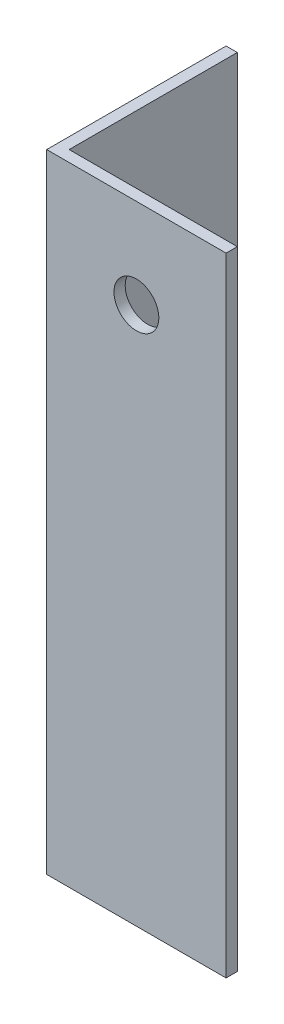
SolidWorks part; units mm, degrees
ref_plane "Front Plane" through (0, 0, 0) normal (0, 0, 1) x (1, 0, 0)
ref_plane "Top Plane" through (0, 0, 0) normal (0, 1, 0) x (1, 0, 0)
ref_plane "Right Plane" through (0, 0, 0) normal (1, 0, 0) x (0, 0, -1)
sketch "Sketch1" plane through (0, 0, 0) normal (0, 1, 0) x (1, 0, 0)
  line L0 (0, 0) -> (0, 25.4)
  line L1 (0, 25.4) -> (1.5875, 25.4)
  line L2 (1.5875, 25.4) -> (1.5875, 1.5875)
  line L3 (1.5875, 1.5875) -> (25.4, 1.5875)
  line L4 (25.4, 1.5875) -> (25.4, 0)
  line L5 (25.4, 0) -> (0, 0)
  dimension "D1" = 1.5875
  dimension "D2" = 25.4
extrude "Boss-Extrude1" add sketch "Sketch1" along normal blind 88.9
sketch "Sketch2" plane through (0, 0, 0) normal (-1, 0, 0) x (0, 0, 1)
  line L0 (-25.4, 0) -> (0, 0) construction
  line L1 (-25.4, 88.9) -> (-25.4, 0) construction
  circle A0 centre (-12.7, 38.1) radius 2.54
  circle A1 centre (-12.7, 12.7) radius 2.54
  dimension "D1" = 12.7
  dimension "D4" = 5.08
  dimension "D2" = 25.4
  dimension "D3" = 12.7
extrude "Cut-Extrude1" cut sketch "Sketch2" against normal blind 88.9
sketch "Sketch3" plane through (0, 0, -1.5875) normal (0, 0, -1) x (-1, 0, 0)
  line L0 (-25.4, 88.9) -> (-25.4, 0) construction
  line L1 (-25.4, 88.9) -> (-1.5875, 88.9) construction
  circle A0 centre (-12.7, 76.2) radius 3.175
  dimension "D1" = 12.7
  dimension "D3" = 6.35
  dimension "D2" = 12.7
extrude "Cut-Extrude2" cut sketch "Sketch3" against normal blind 88.9
